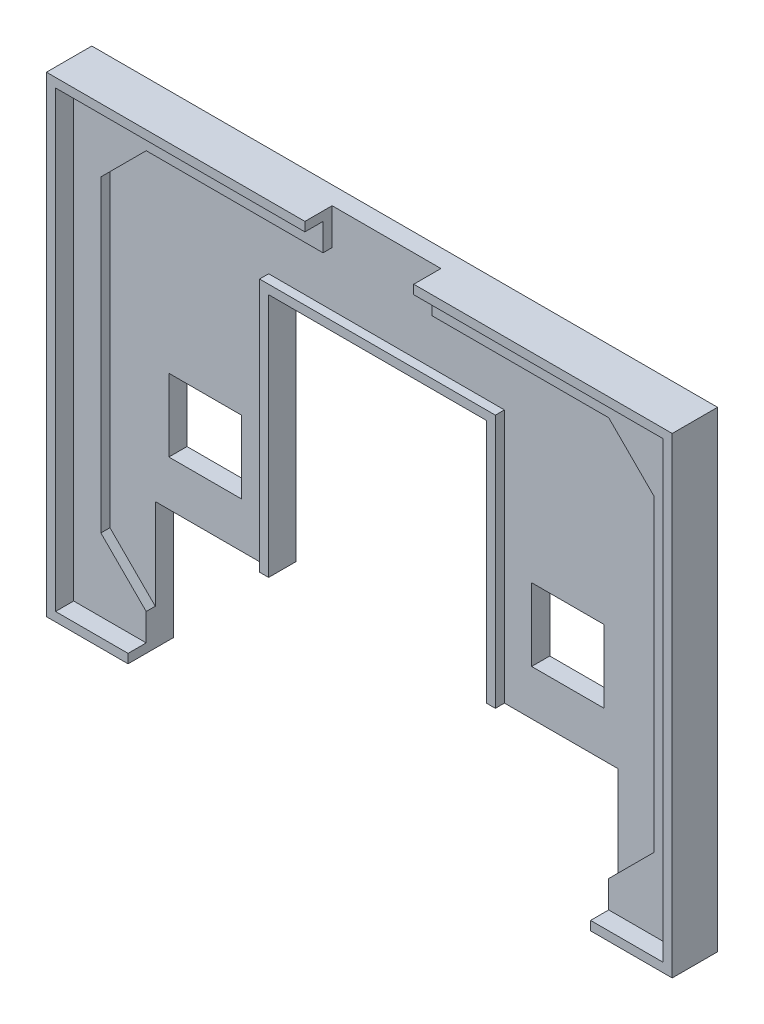
SolidWorks part; units mm, degrees
ref_plane "Přední rovina" through (0, 0, 0) normal (0, 0, 1) x (1, 0, 0)
ref_plane "Horní rovina" through (0, 0, 0) normal (0, 1, 0) x (1, 0, 0)
ref_plane "Pravá rovina" through (0, 0, 0) normal (1, 0, 0) x (0, 0, -1)
sketch "Skica1" plane through (0, 0, 0) normal (0, 0, 1) x (1, 0, 0)
  line L1 (-33.5, -25) -> (33.5, -25)
  line L2 (-33.5, -25) -> (-33.5, 25)
  line L3 (-33.5, 25) -> (33.5, 25)
  line L4 (33.5, -25) -> (33.5, 25)
  line L5 (-33.5, -25) -> (33.5, 25) construction
  line L6 (-33.5, 25) -> (33.5, -25) construction
  point P0 (0, 0)
  dimension "D1" = 67
  dimension "D2" = 50
extrude "Přidat vysunutím1" add sketch "Skica1" along normal blind 3
sketch "Skica2" plane through (0, 0, 3) normal (0, 0, 1) x (1, 0, 0)
  line L0 (-1000, 0) -> (49000, 0) construction
  line L1 (0, -1000) -> (0, 49000) construction
  line L2 (-1000, -22) -> (49000, -22) construction
  line L3 (-25.5, -1000) -> (-25.5, 49000) construction
  line L4 (-30.5, -1000) -> (-30.5, 49000) construction
  line L6 (-33.5, -25) -> (33.5, -25) construction
  line L7 (-25.5, -22) -> (-30.5, -17)
  line L8 (-30.5, -17) -> (-30.5, 17)
  line L9 (-25.5, -22) -> (25.5, -22)
  line L10 (30.5, -17) -> (30.5, 17)
  line L11 (25.5, -22) -> (30.5, -17)
  line L12 (25.5, 22) -> (30.5, 17)
  line L13 (-25.5, 22) -> (25.5, 22)
  line L14 (-25.5, 22) -> (-30.5, 17)
  point P20 (0, -22)
  point P21 (30.5, 0)
  point P24 (-30.5, 0)
  dimension "D1" = 30.5
  dimension "D2" = 5
  dimension "D3" = 3
  dimension "D4" = 45
extrude "Odebrat vysunutím1" cut sketch "Skica2" against normal offset from surface (1 mm away) 2 up to face at (0, 0, 0)
sketch "Skica3" plane through (0, 0, 0) normal (0, 0, -1) x (-1, 0, 0)
  line L0 (0, -1000) -> (0, 49000) construction
  line L1 (33.5, -25) -> (-33.5, -25) construction
  line L2 (24, 1) -> (16, 1)
  line L3 (24, 1) -> (24, -7)
  line L4 (24, -7) -> (16, -7)
  line L5 (16, 1) -> (16, -7)
  line L6 (-16, 1) -> (-16, -7)
  line L7 (33.5, -25) -> (-33.5, -25) construction
  line L8 (25.5, -25) -> (-25.5, -25)
  line L9 (25.5, -25) -> (25.5, -12)
  line L11 (-25.5, -25) -> (-25.5, -12)
  line L12 (-24, -7) -> (-16, -7)
  line L13 (25.5, -12) -> (12, -12)
  line L15 (12, -12) -> (12, 15)
  line L16 (12, 15) -> (-12, 15)
  line L17 (-12, -12) -> (-12, 15)
  line L18 (-12, -12) -> (-25.5, -12)
  line L19 (-24, 1) -> (-24, -7)
  line L20 (-24, 1) -> (-16, 1)
  dimension "D1" = 16
  dimension "D2" = 8
  dimension "D3" = 18
  dimension "D4" = 13
  dimension "D5" = 51
  dimension "D6" = 24
  dimension "D7" = 27
extrude "Odebrat vysunutím2" cut sketch "Skica3" against normal through all
sketch "Skica4" plane through (0, 0, 2) normal (0, 0, 1) x (1, 0, 0)
  line L0 (12, 15) -> (12, -12) construction
  line L1 (-12, -12) -> (-12, 15) construction
  line L2 (-12, 15) -> (12, 15) construction
  line L3 (12, 15) -> (12, -12)
  line L4 (-12, -12) -> (-12, 15)
  line L5 (-12, 15) -> (12, 15)
extrude "Vysunout tenkostěnný1" add sketch "Skica4" along normal up to surface (1 mm away) thin up to face at (0, -3.5714, 3) thin type one direction reverse wall 1
sketch "Skica5" plane through (0, 0, 0) normal (0, 0, -1) x (-1, 0, 0)
  line L0 (-33.5, 25) -> (33.5, 25) construction
  line L1 (33.5, 25) -> (33.5, -25) construction
  line L2 (33.5, -25) -> (25.5, -25) construction
  line L3 (-33.5, -25) -> (-33.5, 25) construction
  line L4 (-25.5, -25) -> (-33.5, -25) construction
  line L5 (-33.5, 25) -> (33.5, 25)
  line L6 (33.5, 25) -> (33.5, -25)
  line L7 (33.5, -25) -> (25.5, -25)
  line L8 (-33.5, -25) -> (-33.5, 25)
  line L9 (-25.5, -25) -> (-33.5, -25)
extrude "Vysunout tenkostěnný2" add sketch "Skica5" against normal blind 5 thin thin type one direction reverse wall 1
sketch "Skica6" plane through (0, 0, 2) normal (0, 0, 1) x (1, 0, 0)
  line L0 (0, -1000) -> (0, 49000) construction
  line L1 (25.5, 22) -> (-25.5, 22) construction
  line L2 (-6, 22) -> (6, 22)
  line L3 (-6, 22) -> (-6, 26)
  line L4 (-6, 26) -> (6, 26)
  line L5 (6, 22) -> (6, 26)
  line L6 (34.5, 26) -> (-34.5, 26) construction
  dimension "D1" = 12
extrude "Odebrat vysunutím3" cut sketch "Skica6" along normal through all
sketch "Skica7" plane through (0, 0, 0) normal (0, 0, -1) x (-1, 0, 0)
  line L0 (-412.4785, -204.4844) -> (-71.1451, -204.4844) construction
  line L1 (-32.44, 14.5405) -> (-23.4595, 23.94)
  line L2 (-23.4595, 23.94) -> (-14.06, 14.9595)
  line L3 (-14.06, 14.9595) -> (-23.0405, 5.56)
  line L4 (-23.0405, 5.56) -> (-32.44, 14.5405)
  line L5 (-34.5, 26) -> (34.5, 26) construction
  line L6 (0, 0) -> (0, 28.27) construction
  line L7 (-34.5, -26) -> (-34.5, 26) construction
  line L8 (14.06, 14.9595) -> (23.0405, 5.56)
  line L9 (23.4595, 23.94) -> (14.06, 14.9595)
  line L10 (32.44, 14.5405) -> (23.4595, 23.94)
  line L11 (23.0405, 5.56) -> (32.44, 14.5405)
  dimension "D1" = 13
  dimension "D2" = 13
  dimension "D3" = 2.06
  dimension "D4" = 2.06
  dimension "D5" = 2.06
extrude "Odebrat vysunutím5" cut sketch "Skica7" against normal blind 1
sketch "Skica8" plane through (0, 0, 0) normal (0, 0, -1) x (-1, 0, 0)
  line L0 (-29.2669, 14.9665) -> (-27.4593, 13.2395)
  line L1 (-27.4593, 13.2395) -> (-25.7323, 15.0471)
  line L2 (-25.7323, 15.0471) -> (-27.5399, 16.7741)
  line L3 (-27.5399, 16.7741) -> (-29.2669, 14.9665)
  line L4 (-32.44, 14.5405) -> (-23.0405, 5.56) construction
  line L5 (-23.4595, 23.94) -> (-32.44, 14.5405) construction
  line L6 (-25.4675, 18.9432) -> (-23.6599, 17.2162)
  line L7 (-23.6599, 17.2162) -> (-21.9329, 19.0238)
  line L8 (-21.9329, 19.0238) -> (-23.7405, 20.7508)
  line L9 (-23.7405, 20.7508) -> (-25.4675, 18.9432)
  line L10 (-14.06, 14.9595) -> (-23.4595, 23.94) construction
  line L11 (-18.3338, 16.2767) -> (-24.551, 9.7693)
  line L12 (-24.551, 9.7693) -> (-26.3586, 11.4963)
  line L13 (-23.4595, 23.94) -> (-32.44, 14.5405) construction
  line L14 (-26.3586, 11.4963) -> (-20.1414, 18.0037)
  line L15 (-20.1414, 18.0037) -> (-18.3338, 16.2767)
  line L16 (-32.44, 14.5405) -> (-23.0405, 5.56) construction
  line L17 (0, 0) -> (0, 27.7759) construction
  line L18 (21.9329, 19.0238) -> (23.7405, 20.7508)
  line L19 (23.6599, 17.2162) -> (21.9329, 19.0238)
  line L20 (25.4675, 18.9432) -> (23.6599, 17.2162)
  line L21 (23.7405, 20.7508) -> (25.4675, 18.9432)
  line L22 (25.7323, 15.0471) -> (27.5399, 16.7741)
  line L23 (27.4593, 13.2395) -> (25.7323, 15.0471)
  line L24 (29.2669, 14.9665) -> (27.4593, 13.2395)
  line L25 (27.5399, 16.7741) -> (29.2669, 14.9665)
  line L26 (18.3338, 16.2767) -> (24.551, 9.7693)
  line L27 (20.1414, 18.0037) -> (18.3338, 16.2767)
  line L28 (26.3586, 11.4963) -> (20.1414, 18.0037)
  line L29 (24.551, 9.7693) -> (26.3586, 11.4963)
  point P22 (-18.7598, 19.4498)
  dimension "D1" = 2.5
  dimension "2,5" = 2.5
  dimension "D2" = 2.5
  dimension "D3" = 2
  dimension "D4" = 2.5
  dimension "D5" = 2.5
  dimension "D6" = 2.5
  dimension "D7" = 2.5
  dimension "D8" = 2.5
  dimension "D9" = 2
  dimension "D10" = 2.5
  dimension "D11" = 2.5
  dimension "D12" = 2
  dimension "D13" = 2
  dimension "D14" = 2
  dimension "D15" = 2
extrude "Přidat vysunutím3" add sketch "Skica8" along normal blind 1 from offset 1 offset against normal yes
sketch "Skica9" plane through (0, 0, 0) normal (0, 0, -1) x (-1, 0, 0)
  line L0 (61.1241, 288.738) -> (530.4575, 288.738) construction
  line L1 (-10.8, 23.3) -> (-6.8, 23.3)
  line L2 (-6.8, 23.3) -> (-6.8, 22.5)
  line L3 (-6.8, 22.5) -> (-6, 22.5)
  line L4 (-6, 22.5) -> (-6, 18.5)
  line L5 (-6, 18.5) -> (-6.8, 18.5)
  line L6 (-6.8, 18.5) -> (-6.8, 17.7)
  line L7 (-6.8, 17.7) -> (-10.8, 17.7)
  line L8 (-10.8, 17.7) -> (-10.8, 23.3)
  line L9 (-4.4, 23.3) -> (-1.2, 23.3)
  line L10 (-1.2, 23.3) -> (-1.2, 22.5)
  line L11 (-1.2, 22.5) -> (-0.4, 22.5)
  line L12 (-0.4, 22.5) -> (-0.4, 17.7)
  line L13 (-0.4, 17.7) -> (-2, 17.7)
  line L14 (-2, 17.7) -> (-2, 20.1)
  line L15 (-2, 20.1) -> (-3.6, 20.1)
  line L16 (-3.6, 20.1) -> (-3.6, 17.7)
  line L17 (-3.6, 17.7) -> (-5.2, 17.7)
  line L18 (-5.2, 17.7) -> (-5.2, 22.5)
  line L19 (-5.2, 22.5) -> (-4.4, 22.5)
  line L20 (-4.4, 22.5) -> (-4.4, 23.3)
  line L21 (1.2, 23.3) -> (4.4, 23.3)
  line L22 (4.4, 23.3) -> (4.4, 22.5)
  line L23 (4.4, 22.5) -> (5.2, 22.5)
  line L24 (5.2, 22.5) -> (5.2, 21.7)
  line L25 (5.2, 21.7) -> (3.6, 21.7)
  line L26 (3.6, 21.7) -> (3.6, 22.4954)
  line L27 (3.6, 22.4954) -> (2, 22.4954)
  line L28 (2, 22.4954) -> (2, 20.8954)
  line L29 (2, 20.8954) -> (4.4, 20.8954)
  line L30 (4.4, 20.8954) -> (4.4, 20.0954)
  line L31 (4.4, 20.0954) -> (5.2, 20.0954)
  line L32 (5.2, 20.0954) -> (5.2, 18.5)
  line L33 (5.2, 18.5) -> (4.4, 18.5)
  line L34 (4.4, 18.5) -> (4.4, 17.7)
  line L35 (4.4, 17.7) -> (1.2, 17.7)
  line L36 (1.2, 17.7) -> (1.2, 18.5)
  line L37 (1.2, 18.5) -> (0.4, 18.5)
  line L38 (0.4, 18.5) -> (0.4, 19.3)
  line L39 (0.4, 19.3) -> (2, 19.3)
  line L40 (2, 19.3) -> (2, 18.5)
  line L41 (2, 18.5) -> (3.6, 18.5)
  line L42 (3.6, 18.5) -> (3.6, 20.0954)
  line L43 (3.6, 20.0954) -> (1.2, 20.0954)
  line L44 (1.2, 20.0954) -> (1.2, 20.9)
  line L45 (1.2, 20.9) -> (0.4, 20.9)
  line L46 (0.4, 20.9) -> (0.4, 22.5)
  line L47 (0.4, 22.5) -> (1.2, 22.5)
  line L48 (1.2, 22.5) -> (1.2, 23.3)
  line L49 (6, 23.3) -> (7.6, 23.3)
  line L50 (7.6, 23.3) -> (7.6, 20.9)
  line L51 (7.6, 20.9) -> (9.2, 20.9)
  line L52 (9.2, 20.9) -> (9.2, 23.3)
  line L53 (9.2, 23.3) -> (10.8, 23.3)
  line L54 (10.8, 23.3) -> (10.8, 17.7)
  line L55 (10.8, 17.7) -> (9.2, 17.7)
  line L56 (9.2, 17.7) -> (9.2, 20.1)
  line L57 (9.2, 20.1) -> (7.6, 20.1)
  line L58 (7.6, 20.1) -> (7.6, 17.7)
  line L59 (7.6, 17.7) -> (6, 17.7)
  line L60 (6, 17.7) -> (6, 23.3)
  line L61 (-34.5, 26) -> (34.5, 26) construction
  dimension "D1" = 0.8
  dimension "D2" = 0.8
  dimension "D3" = 0.8
  dimension "D4" = 0.8
  dimension "D5" = 4
  dimension "D6" = 5.6
  dimension "D7" = 4
  dimension "D8" = 2.7
  dimension "D9" = 1.2
  dimension "D10" = 0.8
  dimension "D11" = 3.2
  dimension "D12" = 0.8
  dimension "D13" = 0.8
  dimension "D14" = 1.6
  dimension "D15" = 1.6
  dimension "D16" = 4.8
  dimension "D17" = 4.8
  dimension "D18" = 0.8
  dimension "D19" = 3.2
  dimension "D20" = 0.8
  dimension "D21" = 0.8
  dimension "D22" = 0.8
  dimension "D23" = 0.8046
  dimension "D24" = 0.8
  dimension "D25" = 0.8
  dimension "D26" = 0.8
  dimension "D27" = 1.6
  dimension "D28" = 0.8
  dimension "D29" = 1.6
  dimension "D30" = 0.8
  dimension "D31" = 0.8
  dimension "D32" = 3.2
  dimension "D33" = 0.8
  dimension "D34" = 0.8
  dimension "D35" = 2.4
  dimension "D36" = 3.2
  dimension "D37" = 0.8
  dimension "D38" = 0.8
  dimension "D39" = 1.6
  dimension "D40" = 0.8
  dimension "D41" = 0.8
  dimension "D42" = 0.8
  dimension "D43" = 1.6
  dimension "D44" = 1.6
  dimension "D45" = 0.8
  dimension "D46" = 0.8
  dimension "D47" = 1.6
  dimension "D48" = 1.6
  dimension "D49" = 1.6
  dimension "D50" = 1.6
  dimension "D51" = 1.6
  dimension "D52" = 5.6
  dimension "D53" = 5.6
  dimension "D54" = 0.8
  dimension "D55" = 2.7
  dimension "D56" = 2.7
  dimension "D57" = 2.4
extrude "Odebrat vysunutím7" cut sketch "Skica9" against normal blind 1
sketch "Skica10" plane through (0, 0, 0) normal (0, 0, -1) x (-1, 0, 0)
  line L0 (-6.8, 23.3) -> (-10.8, 23.3) construction
  line L1 (-9.2, 22.5) -> (-7.6, 22.5)
  line L2 (-9.2, 22.5) -> (-9.2, 18.5)
  line L3 (-9.2, 18.5) -> (-7.6, 18.5)
  line L4 (-7.6, 22.5) -> (-7.6, 18.5)
  line L5 (-6, 18.5) -> (-6, 22.5) construction
  line L6 (-10.8, 17.7) -> (-6.8, 17.7) construction
  line L7 (-10.8, 23.3) -> (-10.8, 17.7) construction
  line L8 (-1.2, 23.3) -> (-4.4, 23.3) construction
  line L9 (-3.6, 22.5) -> (-2, 22.5)
  line L10 (-3.6, 22.5) -> (-3.6, 20.9)
  line L11 (-3.6, 20.9) -> (-2, 20.9)
  line L12 (-2, 22.5) -> (-2, 20.9)
  line L13 (-5.2, 22.5) -> (-5.2, 17.7) construction
  line L14 (-0.4, 17.7) -> (-0.4, 22.5) construction
  line L15 (-3.6, 20.1) -> (-2, 20.1) construction
  dimension "D1" = 0.8
  dimension "D2" = 1.6
  dimension "D3" = 0.8
  dimension "D4" = 1.6
  dimension "D5" = 0.8
  dimension "D6" = 1.6
  dimension "D7" = 1.6
  dimension "D8" = 0.8
extrude "Přidat vysunutím4" add sketch "Skica10" along normal blind 1 from offset 1 offset against normal yes
